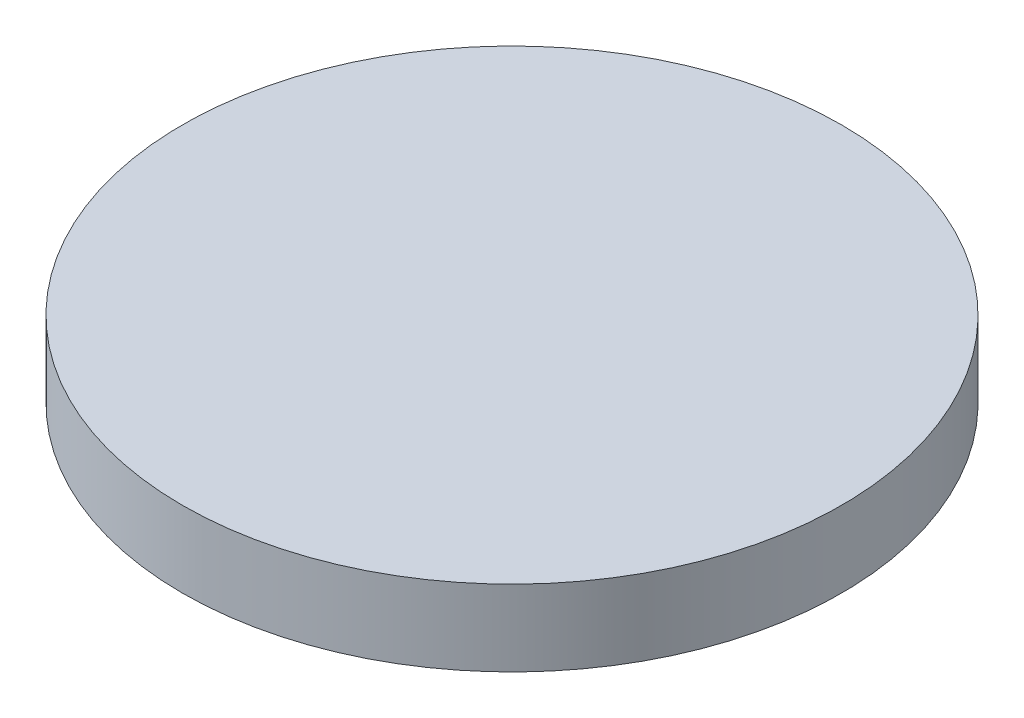
SolidWorks part; units mm, degrees
ref_plane "Front Plane" through (0, 0, 0) normal (0, 0, 1) x (1, 0, 0)
ref_plane "Top Plane" through (0, 0, 0) normal (0, 1, 0) x (1, 0, 0)
ref_plane "Right Plane" through (0, 0, 0) normal (1, 0, 0) x (0, 0, -1)
sketch "Sketch1" plane through (0, 0, 0) normal (0, 1, 0) x (1, 0, 0)
  circle A0 centre (0, 0) radius 13
  dimension "D1" = 26
extrude "Boss-Extrude1" add sketch "Sketch1" along normal blind 3
